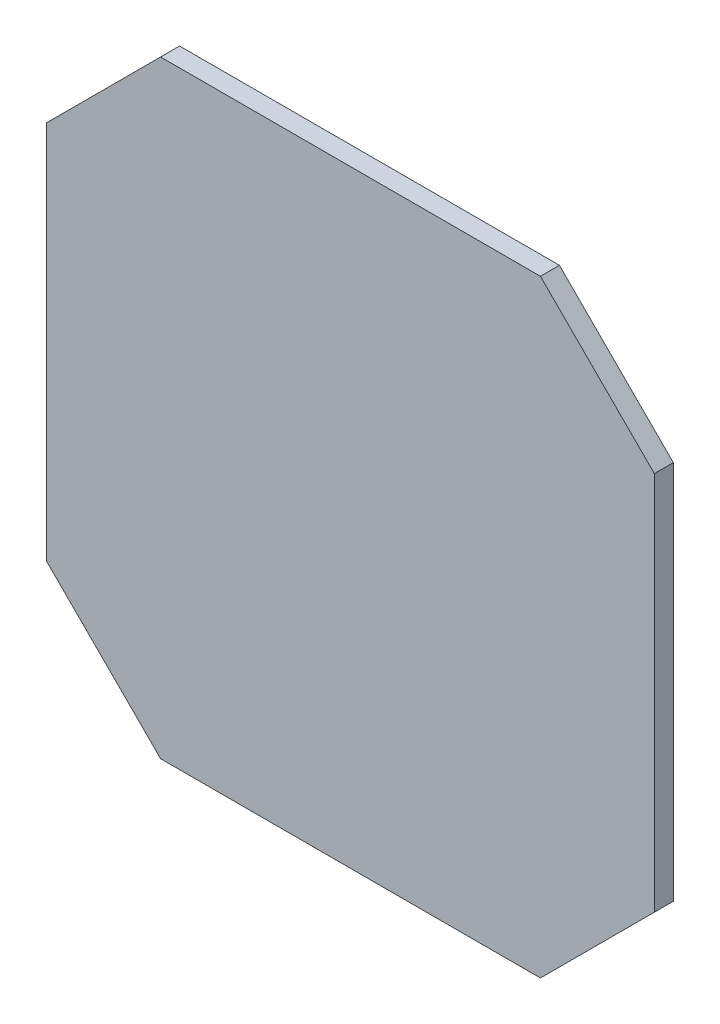
SolidWorks part; units mm, degrees
ref_plane "Front Plane" through (0, 0, 0) normal (0, 0, 1) x (1, 0, 0)
ref_plane "Top Plane" through (0, 0, 0) normal (0, 1, 0) x (1, 0, 0)
ref_plane "Right Plane" through (0, 0, 0) normal (1, 0, 0) x (0, 0, -1)
sketch "Sketch1" plane through (0, 0, 0) normal (0, 0, 1) x (1, 0, 0)
  line L8 (-80, -50) -> (-50, -80)
  line L9 (-50, -80) -> (50, -80)
  line L10 (50, -80) -> (80, -50)
  line L11 (80, -50) -> (80, 50)
  line L12 (80, 50) -> (50, 80)
  line L13 (50, 80) -> (-50, 80)
  line L14 (-50, 80) -> (-80, 50)
  line L15 (-80, 50) -> (-80, -50)
  line L16 (-80, -50) -> (-50, -80)
  line L17 (-50, -80) -> (50, -80)
  line L18 (50, -80) -> (80, -50)
  line L19 (80, -50) -> (80, 50)
  line L20 (80, 50) -> (50, 80)
  line L21 (50, 80) -> (-50, 80)
  line L22 (-50, 80) -> (-80, 50)
  line L23 (-80, 50) -> (-80, -50)
  dimension "D1" = 0
extrude "Boss-Extrude1" add sketch "Sketch1" along normal blind 5
